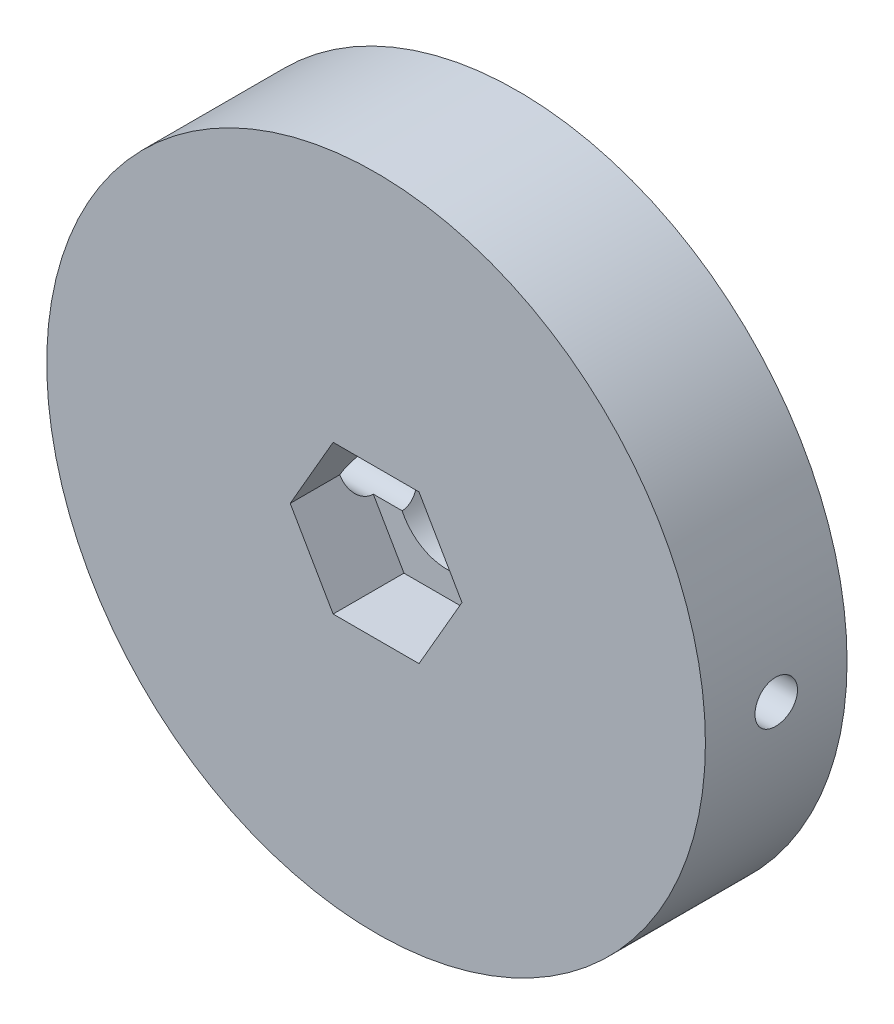
SolidWorks part; units mm, degrees
ref_plane "Спереди" through (0, 0, 0) normal (0, 0, 1) x (1, 0, 0)
ref_plane "Сверху" through (0, 0, 0) normal (0, 1, 0) x (1, 0, 0)
ref_plane "Справа" through (0, 0, 0) normal (1, 0, 0) x (0, 0, -1)
sketch "Эскиз1" plane through (0, 0, 0) normal (0, 0, 1) x (1, 0, 0)
  circle A0 centre (0, 0) radius 23.25
  circle A1 centre (0, 0) radius 3.5
  dimension "D1" = 46.5
  dimension "D2" = 7
extrude "Бобышка-Вытянуть1" add sketch "Эскиз1" along normal blind 10
sketch "Эскиз2" plane through (0, 0, 0) normal (1, 0, 0) x (0, 0, -1)
  line L0 (0, 0) -> (-10, 0) construction
  line L1 (0, -23.25) -> (0, 23.25) construction
  line L2 (-10, 23.25) -> (-10, -23.25) construction
  circle A0 centre (-5, 0) radius 1.5
  dimension "D1" = 3
extrude "Вырез-Вытянуть1" cut sketch "Эскиз2" against normal through all and the other way through all
sketch "Эскиз3" plane through (0, 0, 10) normal (0, 0, 1) x (1, 0, 0)
  line L1 (3.0311, 5.25) -> (-3.0311, 5.25)
  line L2 (-3.0311, 5.25) -> (-6.0622, 0)
  line L3 (-6.0622, 0) -> (-3.0311, -5.25)
  line L4 (-3.0311, -5.25) -> (3.0311, -5.25)
  line L5 (3.0311, -5.25) -> (6.0622, 0)
  line L6 (6.0622, 0) -> (3.0311, 5.25)
  circle A0 centre (0, 0) radius 5.25 construction
  dimension "D1" = 10.5
extrude "Вырез-Вытянуть3" cut sketch "Эскиз3" against normal blind 5
